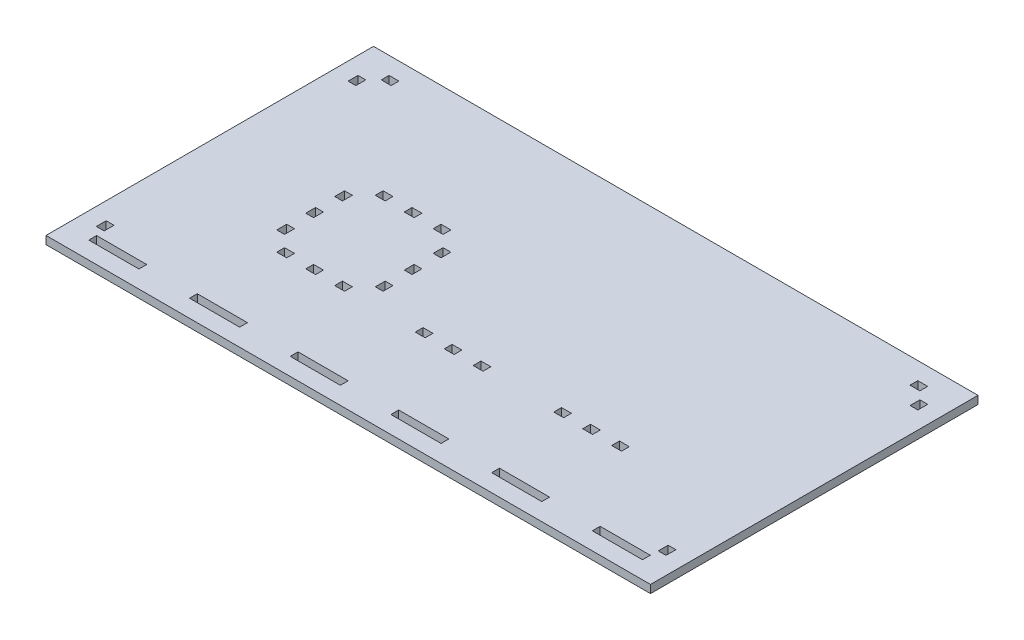
SolidWorks part; units mm, degrees
ref_plane "Front Plane" through (0, 0, 0) normal (0, 0, 1) x (1, 0, 0)
ref_plane "Top Plane" through (0, 0, 0) normal (0, 1, 0) x (1, 0, 0)
ref_plane "Right Plane" through (0, 0, 0) normal (1, 0, 0) x (0, 0, -1)
sketch "Sketch1" plane through (0, 0, 0) normal (0, 1, 0) x (1, 0, 0)
  line L0 (0, 65) -> (0, -65) construction
  line L1 (-120, 65) -> (120, 65)
  line L2 (-120, 65) -> (-120, -65)
  line L3 (-120, -65) -> (120, -65)
  line L4 (120, 65) -> (120, -65)
  line L5 (-111.5875, 55) -> (-111.5875, 45) construction
  line L6 (-113.175, 55) -> (-110, 55) construction
  line L7 (-113.175, 55) -> (-113.175, 45) construction
  line L8 (-113.175, 45) -> (-110, 45) construction
  line L9 (-110, 55) -> (-110, 45) construction
  line L10 (-110, 58.175) -> (-100, 58.175) construction
  line L11 (-110, 58.175) -> (-110, 55) construction
  line L12 (-110, 55) -> (-100, 55) construction
  line L13 (-100, 58.175) -> (-100, 55) construction
  line L14 (-110, 56.5875) -> (-100, 56.5875) construction
  line L15 (100, 56.5875) -> (110, 56.5875) construction
  line L16 (-113.175, 52) -> (-110, 52)
  line L17 (-113.175, 52) -> (-113.175, 48)
  line L18 (-113.175, 48) -> (-110, 48)
  line L19 (-110, 52) -> (-110, 48)
  line L20 (-113.175, 52) -> (-110, 48) construction
  line L21 (-113.175, 48) -> (-110, 52) construction
  line L22 (-107, 55) -> (-103, 55)
  line L23 (-107, 55) -> (-107, 58.175)
  line L24 (-107, 58.175) -> (-103, 58.175)
  line L25 (-103, 55) -> (-103, 58.175)
  line L26 (-107, 55) -> (-103, 58.175) construction
  line L27 (-107, 58.175) -> (-103, 55) construction
  line L28 (110, 55) -> (113.175, 55) construction
  line L29 (110, 55) -> (110, 45) construction
  line L30 (110, 45) -> (113.175, 45) construction
  line L31 (113.175, 55) -> (113.175, 45) construction
  line L32 (100, 58.175) -> (110, 58.175) construction
  line L33 (100, 58.175) -> (100, 55) construction
  line L34 (100, 55) -> (110, 55) construction
  line L35 (110, 58.175) -> (110, 55) construction
  line L36 (111.5875, 55) -> (111.5875, 45) construction
  line L37 (-111.5875, -45) -> (-111.5875, -55) construction
  line L38 (103, 55) -> (107, 55)
  line L39 (103, 55) -> (103, 58.175)
  line L40 (103, 58.175) -> (107, 58.175)
  line L41 (107, 55) -> (107, 58.175)
  line L42 (103, 55) -> (107, 58.175) construction
  line L43 (103, 58.175) -> (107, 55) construction
  line L44 (110, 52) -> (113.175, 52)
  line L45 (110, 52) -> (110, 48)
  line L46 (110, 48) -> (113.175, 48)
  line L47 (113.175, 52) -> (113.175, 48)
  line L48 (110, 52) -> (113.175, 48) construction
  line L49 (110, 48) -> (113.175, 52) construction
  line L50 (-113.175, -45) -> (-110, -45) construction
  line L51 (-113.175, -45) -> (-113.175, -55) construction
  line L52 (-113.175, -55) -> (-110, -55) construction
  line L53 (-110, -45) -> (-110, -55) construction
  line L54 (111.5875, -45) -> (111.5875, -55) construction
  line L55 (-113.175, -52) -> (-110, -52)
  line L56 (-113.175, -52) -> (-113.175, -48)
  line L57 (-113.175, -48) -> (-110, -48)
  line L58 (-110, -52) -> (-110, -48)
  line L59 (-113.175, -52) -> (-110, -48) construction
  line L60 (-113.175, -48) -> (-110, -52) construction
  line L61 (113.175, -55) -> (110, -55) construction
  line L62 (113.175, -55) -> (113.175, -45) construction
  line L63 (113.175, -45) -> (110, -45) construction
  line L64 (110, -55) -> (110, -45) construction
  line L65 (-70, -58.175) -> (-50, -58.175)
  line L66 (110, -52) -> (113.175, -52)
  line L67 (110, -52) -> (110, -48)
  line L68 (110, -48) -> (113.175, -48)
  line L69 (113.175, -52) -> (113.175, -48)
  line L70 (110, -52) -> (113.175, -48) construction
  line L71 (110, -48) -> (113.175, -52) construction
  line L72 (-110, -55) -> (-90, -55)
  line L73 (-110, -55) -> (-110, -58.175)
  line L74 (-110, -58.175) -> (-90, -58.175)
  line L75 (-90, -55) -> (-90, -58.175)
  line L76 (-70, -55) -> (-70, -58.175)
  line L77 (-70, -55) -> (-50, -55)
  line L78 (-50, -55) -> (-50, -58.175)
  line L79 (-30, -58.175) -> (-10, -58.175)
  line L80 (-30, -55) -> (-30, -58.175)
  line L81 (-30, -55) -> (-10, -55)
  line L82 (-10, -55) -> (-10, -58.175)
  line L83 (10, -58.175) -> (30, -58.175)
  line L84 (10, -55) -> (10, -58.175)
  line L85 (10, -55) -> (30, -55)
  line L86 (30, -55) -> (30, -58.175)
  line L87 (50, -58.175) -> (70, -58.175)
  line L88 (50, -55) -> (50, -58.175)
  line L89 (50, -55) -> (70, -55)
  line L90 (70, -55) -> (70, -58.175)
  line L91 (90, -58.175) -> (110, -58.175)
  line L92 (90, -55) -> (90, -58.175)
  line L93 (90, -55) -> (110, -55)
  line L94 (110, -55) -> (110, -58.175)
  line L191 (-68.5, -21.825) -> (-64.5, -21.825)
  line L192 (-68.5, -21.825) -> (-68.5, -25)
  line L193 (-68.5, -25) -> (-64.5, -25)
  line L194 (-64.5, -21.825) -> (-64.5, -25)
  line L195 (-57, -21.825) -> (-53, -21.825)
  line L196 (-57, -21.825) -> (-57, -25)
  line L197 (-57, -25) -> (-53, -25)
  line L198 (-53, -21.825) -> (-53, -25)
  line L199 (-45.5, -21.825) -> (-41.5, -21.825)
  line L200 (-45.5, -21.825) -> (-45.5, -25)
  line L201 (-45.5, -25) -> (-41.5, -25)
  line L202 (-41.5, -21.825) -> (-41.5, -25)
  line L215 (-57, 17.3) -> (-57, 14.125)
  line L216 (41.5, -25) -> (45.5, -25)
  line L217 (41.5, -25) -> (41.5, -21.825)
  line L218 (41.5, -21.825) -> (45.5, -21.825)
  line L219 (45.5, -25) -> (45.5, -21.825)
  line L220 (53, -25) -> (57, -25)
  line L221 (53, -25) -> (53, -21.825)
  line L222 (53, -21.825) -> (57, -21.825)
  line L223 (57, -25) -> (57, -21.825)
  line L224 (64.5, -25) -> (68.5, -25)
  line L225 (64.5, -25) -> (64.5, -21.825)
  line L226 (64.5, -21.825) -> (68.5, -21.825)
  line L227 (68.5, -25) -> (68.5, -21.825)
  line L240 (-13.5, -21.825) -> (-9.5, -21.825)
  line L241 (-13.5, -21.825) -> (-13.5, -25)
  line L242 (-13.5, -25) -> (-9.5, -25)
  line L243 (-9.5, -21.825) -> (-9.5, -25)
  line L244 (-2, -25) -> (2, -25)
  line L245 (-2, -25) -> (-2, -21.825)
  line L246 (-2, -21.825) -> (2, -21.825)
  line L247 (2, -25) -> (2, -21.825)
  line L248 (9.5, -25) -> (13.5, -25)
  line L249 (9.5, -25) -> (9.5, -21.825)
  line L250 (9.5, -21.825) -> (13.5, -21.825)
  line L251 (13.5, -25) -> (13.5, -21.825)
  line L252 (-68.5, 17.3) -> (-68.5, 14.125)
  line L253 (-68.5, 14.125) -> (-64.5, 14.125)
  line L254 (-64.5, 17.3) -> (-64.5, 14.125)
  line L255 (-41.5, 17.3) -> (-41.5, 14.125)
  line L256 (-41.5, 14.125) -> (-45.5, 14.125)
  line L257 (-45.5, 17.3) -> (-45.5, 14.125)
  line L258 (-57, 14.125) -> (-53, 14.125)
  line L259 (-76.15, 17.3) -> (-33.85, 17.3)
  line L260 (-76.15, 17.3) -> (-76.15, -25)
  line L261 (-76.15, -25) -> (-33.85, -25)
  line L262 (-33.85, 17.3) -> (-33.85, -25)
  line L263 (-76.15, 17.3) -> (-33.85, -25) construction
  line L264 (-76.15, -25) -> (-33.85, 17.3) construction
  line L265 (-53, 17.3) -> (-53, 14.125)
  line L266 (-57, 17.3) -> (-53, 14.125) construction
  line L267 (-57, 14.125) -> (-53, 17.3) construction
  line L268 (-57, 17.3) -> (-53, 17.3)
  line L269 (-57, -21.825) -> (-57, -25)
  line L270 (-68.5, -21.825) -> (-68.5, -25)
  line L271 (-68.5, -25) -> (-64.5, -25)
  line L272 (-64.5, -21.825) -> (-64.5, -25)
  line L273 (-41.5, -21.825) -> (-41.5, -25)
  line L274 (-41.5, -25) -> (-45.5, -25)
  line L275 (-45.5, -21.825) -> (-45.5, -25)
  line L276 (-57, -25) -> (-53, -25)
  line L277 (-53, -21.825) -> (-53, -25)
  line L278 (-57, -21.825) -> (-53, -25) construction
  line L279 (-57, -25) -> (-53, -21.825) construction
  line L280 (-57, -21.825) -> (-53, -21.825)
  line L281 (-45.5, -21.825) -> (-41.5, -21.825)
  line L282 (-68.5, -21.825) -> (-64.5, -21.825)
  line L283 (-76.15, -5.85) -> (-72.975, -5.85)
  line L284 (-76.15, -5.85) -> (-76.15, -1.85)
  line L285 (-76.15, -1.85) -> (-72.975, -1.85)
  line L286 (-72.975, -5.85) -> (-72.975, -1.85)
  line L287 (-76.15, 5.65) -> (-72.975, 5.65)
  line L288 (-76.15, 5.65) -> (-76.15, 9.65)
  line L289 (-76.15, 9.65) -> (-72.975, 9.65)
  line L290 (-72.975, 5.65) -> (-72.975, 9.65)
  line L291 (-55, 17.3) -> (-55, -25) construction
  line L292 (-76.15, -13.35) -> (-72.975, -13.35)
  line L293 (-76.15, -13.35) -> (-76.15, -17.35)
  line L294 (-76.15, -17.35) -> (-72.975, -17.35)
  line L295 (-72.975, -13.35) -> (-72.975, -17.35)
  line L296 (-37.025, -13.35) -> (-37.025, -17.35)
  line L297 (-33.85, -17.35) -> (-37.025, -17.35)
  line L298 (-33.85, -13.35) -> (-37.025, -13.35)
  line L299 (-37.025, 5.65) -> (-37.025, 9.65)
  line L300 (-33.85, 9.65) -> (-37.025, 9.65)
  line L301 (-33.85, 5.65) -> (-37.025, 5.65)
  line L302 (-37.025, -5.85) -> (-37.025, -1.85)
  line L303 (-33.85, -1.85) -> (-37.025, -1.85)
  line L304 (-33.85, -5.85) -> (-37.025, -5.85)
  point P19 (-111.5875, 50)
  point P24 (-105, 56.5875)
  point P41 (105, 56.5875)
  point P46 (111.5875, 50)
  point P57 (-111.5875, -50)
  point P68 (111.5875, -50)
  point P77 (-55, -25)
  point P121 (55, -25)
  point P134 (0, -25)
  point P135 (-55, -25)
  point P144 (-55, 15.7125)
  point P148 (-55, -3.85)
  point P155 (-55, -25)
  point P156 (-55, 17.3)
  point P157 (-55, 17.3)
  point P166 (-55, -23.4125)
  point P182 (-72.975, -3.85)
  point P183 (-76.15, -3.85)
  dimension "D1" = 240
  dimension "D2" = 130
  dimension "D3" = 65
  dimension "D4" = 120
  dimension "D5" = 6.825
  dimension "D6" = 6.825
  dimension "D7" = 10
  dimension "D8" = 10
  dimension "D9" = 3.175
  dimension "D10" = 10
  dimension "D11" = 4
  dimension "D12" = 4
  dimension "D13" = 6.825
  dimension "D14" = 6.825
  dimension "D15" = 10
  dimension "D16" = 10
  dimension "D17" = 10
  dimension "D18" = 3.175
  dimension "D19" = 4
  dimension "D20" = 4
  dimension "D21" = 6.825
  dimension "D22" = 10
  dimension "D23" = 10
  dimension "D24" = 3.175
  dimension "D25" = 4
  dimension "D26" = 6.825
  dimension "D27" = 3.175
  dimension "D28" = 10
  dimension "D29" = 10
  dimension "D30" = 4
  dimension "D31" = 20
  dimension "D32" = 3.175
  dimension "D37" = 4
  dimension "D39" = 3.175
  dimension "D34" = 7.5
  dimension "D35" = 7.5
  dimension "D36" = 55
  dimension "D38" = 4
  dimension "D40" = 3.175
  dimension "D41" = 7.5
  dimension "D42" = 7.5
  dimension "D43" = 55
  dimension "D44" = 30
  dimension "D45" = 30
  dimension "D46" = 4
  dimension "D47" = 3.175
  dimension "D48" = 7.5
  dimension "D49" = 7.5
  dimension "D50" = 30
  dimension "D51" = 42.3
  dimension "D52" = 42.3
  dimension "D53" = 4
  dimension "D54" = 3.175
  dimension "D55" = 7.5
  dimension "D56" = 7.5
  dimension "D57" = 4
  dimension "D58" = 3.175
  dimension "D59" = 7.5
  dimension "D60" = 7.5
  dimension "D61" = 3.175
  dimension "D62" = 7.5
  dimension "D63" = 7.5
  dimension "D33" = 6
extrude "Boss-Extrude1" add sketch "Sketch1" along normal blind 3.175 contours L4 L1 L2 L3 L251 L248 L249 L250 L247 L244 L245 L246 L227 L224 L225 L226 L223 L220 L221 L222 L219 L216 L217 L218 L69 L66 L67 L68 L58 L55 L56 L57 L41 L38 L39 L40 L25 L22 L23 L24 L16 | L262 L304 L302 L303 L301 L299 L300 L259 L255 L256 L257 L265 L258 L215 L254 L253 L252 L260 L289 L290 L287 L285 L286 L283 L292 L295 L294 L261 L192 L191 L194 L196 L195 L198 L200 L199 L202 L297 L296
sketch "Sketch2" plane through (0, 3.175, 0) normal (0, 1, 0) x (1, 0, 0)
  line L8 (120.0406, -65.0406) -> (120.0406, 65.0406)
  line L9 (120.0406, 65.0406) -> (-120.0406, 65.0406)
  line L10 (-120.0406, 65.0406) -> (-120.0406, -65.0406)
  line L11 (-120.0406, -65.0406) -> (120.0406, -65.0406)
  line L12 (120.0406, -65.0406) -> (120.0406, 65.0406)
  line L13 (120.0406, 65.0406) -> (-120.0406, 65.0406)
  line L14 (-120.0406, 65.0406) -> (-120.0406, -65.0406)
  line L15 (-120.0406, -65.0406) -> (120.0406, -65.0406)
  line L21 (-33.8906, 5.6906) -> (-33.8906, 9.6094)
  line L22 (-73.0156, -1.8906) -> (-76.1094, -1.8906)
  line L23 (-73.0156, -5.8094) -> (-73.0156, -1.8906)
  line L24 (-76.1094, -5.8094) -> (-73.0156, -5.8094)
  line L25 (-76.1094, -1.8906) -> (-76.1094, -5.8094)
  line L26 (-103.0406, 55.0406) -> (-103.0406, 58.1344)
  line L27 (-106.9594, 55.0406) -> (-103.0406, 55.0406)
  line L28 (-106.9594, 58.1344) -> (-106.9594, 55.0406)
  line L29 (-103.0406, 58.1344) -> (-106.9594, 58.1344)
  line L30 (-103.0406, 55.0406) -> (-103.0406, 58.1344)
  line L31 (-106.9594, 55.0406) -> (-103.0406, 55.0406)
  line L32 (-106.9594, 58.1344) -> (-106.9594, 55.0406)
  line L33 (-103.0406, 58.1344) -> (-106.9594, 58.1344)
  line L34 (-73.0156, -1.8906) -> (-76.1094, -1.8906)
  line L35 (-73.0156, -5.8094) -> (-73.0156, -1.8906)
  line L36 (-76.1094, -5.8094) -> (-73.0156, -5.8094)
  line L37 (-76.1094, -1.8906) -> (-76.1094, -5.8094)
  line L38 (-36.9844, 5.6906) -> (-33.8906, 5.6906)
  line L39 (-33.8906, 9.6094) -> (-36.9844, 9.6094)
  line L40 (-36.9844, 9.6094) -> (-36.9844, 5.6906)
  line L41 (-33.8906, 5.6906) -> (-33.8906, 9.6094)
  line L42 (-36.9844, 5.6906) -> (-33.8906, 5.6906)
  line L43 (-33.8906, 9.6094) -> (-36.9844, 9.6094)
  line L44 (-113.1344, 48.0406) -> (-110.0406, 48.0406)
  line L45 (-110.0406, 48.0406) -> (-110.0406, 51.9594)
  line L46 (-110.0406, 51.9594) -> (-113.1344, 51.9594)
  line L47 (-113.1344, 51.9594) -> (-113.1344, 48.0406)
  line L48 (-113.1344, 48.0406) -> (-110.0406, 48.0406)
  line L49 (-110.0406, 48.0406) -> (-110.0406, 51.9594)
  line L50 (-110.0406, 51.9594) -> (-113.1344, 51.9594)
  line L51 (-113.1344, 51.9594) -> (-113.1344, 48.0406)
  line L52 (-36.9844, 9.6094) -> (-36.9844, 5.6906)
  line L54 (-9.5406, -24.9594) -> (-9.5406, -21.8656)
  line L55 (-13.4594, -24.9594) -> (-9.5406, -24.9594)
  line L56 (-73.0156, -17.3094) -> (-73.0156, -13.3906)
  line L57 (-76.1094, -13.3906) -> (-76.1094, -17.3094)
  line L58 (-76.1094, -17.3094) -> (-73.0156, -17.3094)
  line L59 (-73.0156, -13.3906) -> (-76.1094, -13.3906)
  line L60 (-73.0156, -17.3094) -> (-73.0156, -13.3906)
  line L61 (-76.1094, -13.3906) -> (-76.1094, -17.3094)
  line L62 (103.0406, 55.0406) -> (106.9594, 55.0406)
  line L63 (103.0406, 58.1344) -> (103.0406, 55.0406)
  line L64 (106.9594, 58.1344) -> (103.0406, 58.1344)
  line L65 (106.9594, 55.0406) -> (106.9594, 58.1344)
  line L66 (103.0406, 55.0406) -> (106.9594, 55.0406)
  line L67 (103.0406, 58.1344) -> (103.0406, 55.0406)
  line L68 (106.9594, 58.1344) -> (103.0406, 58.1344)
  line L69 (106.9594, 55.0406) -> (106.9594, 58.1344)
  line L70 (-76.1094, -17.3094) -> (-73.0156, -17.3094)
  line L71 (-73.0156, -13.3906) -> (-76.1094, -13.3906)
  line L72 (-13.4594, -21.8656) -> (-13.4594, -24.9594)
  line L73 (-9.5406, -21.8656) -> (-13.4594, -21.8656)
  line L74 (-9.5406, -24.9594) -> (-9.5406, -21.8656)
  line L75 (-13.4594, -24.9594) -> (-9.5406, -24.9594)
  line L76 (-13.4594, -21.8656) -> (-13.4594, -24.9594)
  line L77 (-9.5406, -21.8656) -> (-13.4594, -21.8656)
  line L79 (-33.8906, -5.8094) -> (-33.8906, -1.8906)
  line L80 (110.0406, 48.0406) -> (113.1344, 48.0406)
  line L81 (110.0406, 51.9594) -> (110.0406, 48.0406)
  line L82 (113.1344, 48.0406) -> (113.1344, 51.9594)
  line L83 (113.1344, 51.9594) -> (110.0406, 51.9594)
  line L84 (110.0406, 48.0406) -> (113.1344, 48.0406)
  line L85 (110.0406, 51.9594) -> (110.0406, 48.0406)
  line L86 (113.1344, 48.0406) -> (113.1344, 51.9594)
  line L87 (113.1344, 51.9594) -> (110.0406, 51.9594)
  line L88 (-36.9844, -1.8906) -> (-36.9844, -5.8094)
  line L89 (-36.9844, -5.8094) -> (-33.8906, -5.8094)
  line L90 (-64.5406, 14.1656) -> (-64.5406, 17.2594)
  line L91 (-68.4594, 17.2594) -> (-68.4594, 14.1656)
  line L92 (-68.4594, 14.1656) -> (-64.5406, 14.1656)
  line L93 (-64.5406, 17.2594) -> (-68.4594, 17.2594)
  line L94 (-64.5406, 14.1656) -> (-64.5406, 17.2594)
  line L95 (-68.4594, 17.2594) -> (-68.4594, 14.1656)
  line L96 (-68.4594, 14.1656) -> (-64.5406, 14.1656)
  line L97 (-64.5406, 17.2594) -> (-68.4594, 17.2594)
  line L98 (-33.8906, -1.8906) -> (-36.9844, -1.8906)
  line L99 (-33.8906, -5.8094) -> (-33.8906, -1.8906)
  line L100 (-36.9844, -1.8906) -> (-36.9844, -5.8094)
  line L101 (-36.9844, -5.8094) -> (-33.8906, -5.8094)
  line L102 (-33.8906, -1.8906) -> (-36.9844, -1.8906)
  line L108 (-110.0406, -51.9594) -> (-110.0406, -48.0406)
  line L109 (-113.1344, -51.9594) -> (-110.0406, -51.9594)
  line L110 (-113.1344, -48.0406) -> (-113.1344, -51.9594)
  line L111 (-110.0406, -48.0406) -> (-113.1344, -48.0406)
  line L112 (-110.0406, -51.9594) -> (-110.0406, -48.0406)
  line L113 (-113.1344, -51.9594) -> (-110.0406, -51.9594)
  line L114 (-113.1344, -48.0406) -> (-113.1344, -51.9594)
  line L115 (-110.0406, -48.0406) -> (-113.1344, -48.0406)
  line L116 (-53.0406, 14.1656) -> (-53.0406, 17.2594)
  line L117 (-56.9594, 17.2594) -> (-56.9594, 14.1656)
  line L118 (-56.9594, 14.1656) -> (-53.0406, 14.1656)
  line L119 (-53.0406, 17.2594) -> (-56.9594, 17.2594)
  line L120 (-53.0406, 14.1656) -> (-53.0406, 17.2594)
  line L121 (-56.9594, 17.2594) -> (-56.9594, 14.1656)
  line L122 (-56.9594, 14.1656) -> (-53.0406, 14.1656)
  line L123 (-53.0406, 17.2594) -> (-56.9594, 17.2594)
  line L126 (-109.9594, -55.0406) -> (-109.9594, -58.1344)
  line L127 (-90.0406, -58.1344) -> (-90.0406, -55.0406)
  line L128 (-109.9594, -58.1344) -> (-90.0406, -58.1344)
  line L129 (-90.0406, -55.0406) -> (-109.9594, -55.0406)
  line L130 (-109.9594, -55.0406) -> (-109.9594, -58.1344)
  line L131 (-90.0406, -58.1344) -> (-90.0406, -55.0406)
  line L132 (-109.9594, -58.1344) -> (-90.0406, -58.1344)
  line L133 (-90.0406, -55.0406) -> (-109.9594, -55.0406)
  line L136 (-1.9594, -24.9594) -> (1.9594, -24.9594)
  line L137 (-33.8906, -17.3094) -> (-33.8906, -13.3906)
  line L138 (-36.9844, -17.3094) -> (-33.8906, -17.3094)
  line L139 (-36.9844, -13.3906) -> (-36.9844, -17.3094)
  line L140 (-33.8906, -13.3906) -> (-36.9844, -13.3906)
  line L141 (-33.8906, -17.3094) -> (-33.8906, -13.3906)
  line L142 (-41.5406, 14.1656) -> (-41.5406, 17.2594)
  line L143 (-45.4594, 17.2594) -> (-45.4594, 14.1656)
  line L144 (-50.0406, -58.1344) -> (-50.0406, -55.0406)
  line L145 (-69.9594, -55.0406) -> (-69.9594, -58.1344)
  line L146 (-69.9594, -58.1344) -> (-50.0406, -58.1344)
  line L147 (-50.0406, -55.0406) -> (-69.9594, -55.0406)
  line L148 (-50.0406, -58.1344) -> (-50.0406, -55.0406)
  line L149 (-69.9594, -55.0406) -> (-69.9594, -58.1344)
  line L150 (-69.9594, -58.1344) -> (-50.0406, -58.1344)
  line L151 (-50.0406, -55.0406) -> (-69.9594, -55.0406)
  line L152 (-41.5406, 17.2594) -> (-45.4594, 17.2594)
  line L153 (-45.4594, 14.1656) -> (-41.5406, 14.1656)
  line L154 (-41.5406, 14.1656) -> (-41.5406, 17.2594)
  line L155 (-45.4594, 17.2594) -> (-45.4594, 14.1656)
  line L156 (-41.5406, 17.2594) -> (-45.4594, 17.2594)
  line L157 (-45.4594, 14.1656) -> (-41.5406, 14.1656)
  line L158 (-36.9844, -17.3094) -> (-33.8906, -17.3094)
  line L159 (-36.9844, -13.3906) -> (-36.9844, -17.3094)
  line L160 (-33.8906, -13.3906) -> (-36.9844, -13.3906)
  line L161 (1.9594, -24.9594) -> (1.9594, -21.8656)
  line L162 (-10.0406, -58.1344) -> (-10.0406, -55.0406)
  line L163 (-29.9594, -58.1344) -> (-10.0406, -58.1344)
  line L164 (-29.9594, -55.0406) -> (-29.9594, -58.1344)
  line L165 (-10.0406, -55.0406) -> (-29.9594, -55.0406)
  line L166 (-10.0406, -58.1344) -> (-10.0406, -55.0406)
  line L167 (-29.9594, -58.1344) -> (-10.0406, -58.1344)
  line L168 (-29.9594, -55.0406) -> (-29.9594, -58.1344)
  line L169 (-10.0406, -55.0406) -> (-29.9594, -55.0406)
  line L170 (-1.9594, -21.8656) -> (-1.9594, -24.9594)
  line L171 (1.9594, -21.8656) -> (-1.9594, -21.8656)
  line L172 (-1.9594, -24.9594) -> (1.9594, -24.9594)
  line L173 (1.9594, -24.9594) -> (1.9594, -21.8656)
  line L174 (-1.9594, -21.8656) -> (-1.9594, -24.9594)
  line L175 (1.9594, -21.8656) -> (-1.9594, -21.8656)
  line L176 (-64.5406, -24.9594) -> (-64.5406, -21.8656)
  line L177 (-68.4594, -21.8656) -> (-68.4594, -24.9594)
  line L178 (-64.5406, -21.8656) -> (-68.4594, -21.8656)
  line L179 (-68.4594, -24.9594) -> (-64.5406, -24.9594)
  line L180 (29.9594, -58.1344) -> (29.9594, -55.0406)
  line L181 (10.0406, -55.0406) -> (10.0406, -58.1344)
  line L182 (10.0406, -58.1344) -> (29.9594, -58.1344)
  line L183 (29.9594, -55.0406) -> (10.0406, -55.0406)
  line L184 (29.9594, -58.1344) -> (29.9594, -55.0406)
  line L185 (10.0406, -55.0406) -> (10.0406, -58.1344)
  line L186 (10.0406, -58.1344) -> (29.9594, -58.1344)
  line L187 (29.9594, -55.0406) -> (10.0406, -55.0406)
  line L188 (-64.5406, -24.9594) -> (-64.5406, -21.8656)
  line L189 (-68.4594, -21.8656) -> (-68.4594, -24.9594)
  line L190 (-64.5406, -21.8656) -> (-68.4594, -21.8656)
  line L191 (-68.4594, -24.9594) -> (-64.5406, -24.9594)
  line L198 (69.9594, -58.1344) -> (69.9594, -55.0406)
  line L199 (50.0406, -55.0406) -> (50.0406, -58.1344)
  line L200 (69.9594, -55.0406) -> (50.0406, -55.0406)
  line L201 (50.0406, -58.1344) -> (69.9594, -58.1344)
  line L202 (69.9594, -58.1344) -> (69.9594, -55.0406)
  line L203 (50.0406, -55.0406) -> (50.0406, -58.1344)
  line L204 (69.9594, -55.0406) -> (50.0406, -55.0406)
  line L205 (50.0406, -58.1344) -> (69.9594, -58.1344)
  line L206 (-56.9594, -24.9594) -> (-53.0406, -24.9594)
  line L207 (-53.0406, -24.9594) -> (-53.0406, -21.8656)
  line L208 (-53.0406, -21.8656) -> (-56.9594, -21.8656)
  line L209 (-56.9594, -21.8656) -> (-56.9594, -24.9594)
  line L210 (-56.9594, -24.9594) -> (-53.0406, -24.9594)
  line L211 (-53.0406, -24.9594) -> (-53.0406, -21.8656)
  line L212 (-53.0406, -21.8656) -> (-56.9594, -21.8656)
  line L213 (-56.9594, -21.8656) -> (-56.9594, -24.9594)
  line L218 (13.4594, -24.9594) -> (13.4594, -21.8656)
  line L219 (9.5406, -24.9594) -> (13.4594, -24.9594)
  line L220 (109.9594, -58.1344) -> (109.9594, -55.0406)
  line L221 (90.0406, -55.0406) -> (90.0406, -58.1344)
  line L222 (90.0406, -58.1344) -> (109.9594, -58.1344)
  line L223 (109.9594, -55.0406) -> (90.0406, -55.0406)
  line L224 (109.9594, -58.1344) -> (109.9594, -55.0406)
  line L225 (90.0406, -55.0406) -> (90.0406, -58.1344)
  line L226 (90.0406, -58.1344) -> (109.9594, -58.1344)
  line L227 (109.9594, -55.0406) -> (90.0406, -55.0406)
  line L229 (9.5406, -21.8656) -> (9.5406, -24.9594)
  line L230 (13.4594, -21.8656) -> (9.5406, -21.8656)
  line L231 (13.4594, -24.9594) -> (13.4594, -21.8656)
  line L232 (-45.4594, -24.9594) -> (-41.5406, -24.9594)
  line L233 (-41.5406, -24.9594) -> (-41.5406, -21.8656)
  line L234 (-45.4594, -21.8656) -> (-45.4594, -24.9594)
  line L235 (-41.5406, -21.8656) -> (-45.4594, -21.8656)
  line L236 (-45.4594, -24.9594) -> (-41.5406, -24.9594)
  line L237 (-41.5406, -24.9594) -> (-41.5406, -21.8656)
  line L238 (113.1344, -51.9594) -> (113.1344, -48.0406)
  line L239 (110.0406, -51.9594) -> (113.1344, -51.9594)
  line L240 (110.0406, -48.0406) -> (110.0406, -51.9594)
  line L241 (113.1344, -48.0406) -> (110.0406, -48.0406)
  line L242 (113.1344, -51.9594) -> (113.1344, -48.0406)
  line L243 (110.0406, -51.9594) -> (113.1344, -51.9594)
  line L244 (110.0406, -48.0406) -> (110.0406, -51.9594)
  line L245 (113.1344, -48.0406) -> (110.0406, -48.0406)
  line L246 (-45.4594, -21.8656) -> (-45.4594, -24.9594)
  line L247 (-41.5406, -21.8656) -> (-45.4594, -21.8656)
  line L248 (9.5406, -24.9594) -> (13.4594, -24.9594)
  line L249 (9.5406, -21.8656) -> (9.5406, -24.9594)
  line L250 (13.4594, -21.8656) -> (9.5406, -21.8656)
  line L261 (45.4594, -24.9594) -> (45.4594, -21.8656)
  line L262 (45.4594, -21.8656) -> (41.5406, -21.8656)
  line L263 (41.5406, -21.8656) -> (41.5406, -24.9594)
  line L264 (41.5406, -24.9594) -> (45.4594, -24.9594)
  line L265 (-76.1094, 5.6906) -> (-73.0156, 5.6906)
  line L266 (-73.0156, 5.6906) -> (-73.0156, 9.6094)
  line L267 (-76.1094, 9.6094) -> (-76.1094, 5.6906)
  line L268 (-73.0156, 9.6094) -> (-76.1094, 9.6094)
  line L269 (-76.1094, 5.6906) -> (-73.0156, 5.6906)
  line L270 (-73.0156, 5.6906) -> (-73.0156, 9.6094)
  line L271 (-76.1094, 9.6094) -> (-76.1094, 5.6906)
  line L272 (-73.0156, 9.6094) -> (-76.1094, 9.6094)
  line L273 (45.4594, -24.9594) -> (45.4594, -21.8656)
  line L274 (45.4594, -21.8656) -> (41.5406, -21.8656)
  line L275 (41.5406, -21.8656) -> (41.5406, -24.9594)
  line L276 (41.5406, -24.9594) -> (45.4594, -24.9594)
  line L291 (56.9594, -24.9594) -> (56.9594, -21.8656)
  line L292 (53.0406, -24.9594) -> (56.9594, -24.9594)
  line L293 (56.9594, -21.8656) -> (53.0406, -21.8656)
  line L294 (53.0406, -21.8656) -> (53.0406, -24.9594)
  line L295 (56.9594, -24.9594) -> (56.9594, -21.8656)
  line L296 (53.0406, -24.9594) -> (56.9594, -24.9594)
  line L297 (56.9594, -21.8656) -> (53.0406, -21.8656)
  line L298 (53.0406, -21.8656) -> (53.0406, -24.9594)
  line L309 (68.4594, -24.9594) -> (68.4594, -21.8656)
  line L310 (64.5406, -24.9594) -> (68.4594, -24.9594)
  line L311 (64.5406, -21.8656) -> (64.5406, -24.9594)
  line L312 (68.4594, -21.8656) -> (64.5406, -21.8656)
  line L313 (68.4594, -24.9594) -> (68.4594, -21.8656)
  line L314 (64.5406, -24.9594) -> (68.4594, -24.9594)
  line L315 (64.5406, -21.8656) -> (64.5406, -24.9594)
  line L316 (68.4594, -21.8656) -> (64.5406, -21.8656)
  dimension "D1" = 0.0406
  dimension "D2" = 0.0406
  dimension "D3" = 0.0406
  dimension "D4" = 0.0406
  dimension "D5" = 0.0406
  dimension "D6" = 0.0406
  dimension "D7" = 0.0406
  dimension "D8" = 0.0406
  dimension "D9" = 0.0406
  dimension "D10" = 0.0406
  dimension "D11" = 0.0406
  dimension "D12" = 0.0406
  dimension "D13" = 0.0406
  dimension "D14" = 0.0406
  dimension "D15" = 0.0406
  dimension "D16" = 0.0406
  dimension "D17" = 0.0406
  dimension "D18" = 0.0406
  dimension "D19" = 0.0406
  dimension "D20" = 0.0406
  dimension "D21" = 0.0406
  dimension "D22" = 0.0406
  dimension "D23" = 0.0406
  dimension "D24" = 0.0406
  dimension "D25" = 0.0406
  dimension "D26" = 0.0406
  dimension "D27" = 0.0406
  dimension "D28" = 0.0406
  dimension "D29" = 0.0406
  dimension "D30" = 0.0406
  dimension "D31" = 0.0406
extrude "Boss-Extrude2" add sketch "Sketch2" against normal blind 3.175
equation "\"stepper width\"=4.23"
equation "\"stepper hole disctance\"= 3.1"
equation "\"stepper hole diameter\"=0.34"
equation "\"stepper shaft hole\"=2.4"
equation "\"tooth width\"=0.4"
equation "\"tooth thickness\"=0.3175"
equation "\"tooth to side\"=0.75"
equation "\"motor chamber height\"= 6"
equation "\"enclosure length\"= 22"
equation "\"platform diameter\"= 9cm"
equation "\"teeth width\"=0.3175"
equation "\"teeth lenght\"=2"
equation "\"tower width\"=7.7"
equation "\"D1@Sketch1\"=\"enclosure length\"+2"
equation "\"D2@Sketch1\"=\"enclosure length\"/2+2"
equation "\"D3@Sketch1\"=\"enclosure length\"/4+1"
equation "\"D4@Sketch1\"=\"enclosure length\"/2+1"
equation "\"D5@Sketch1\"=1 - \"tooth thickness\""
equation "\"D6@Sketch1\"=1 - \"tooth thickness\""
equation "\"D9@Sketch1\"=\"teeth width\""
equation "\"support width\"=1"
equation "\"D10@Sketch1\"=\"support width\""
equation "\"D11@Sketch1\"=\"tooth width\""
equation "\"D12@Sketch1\"=\"tooth width\""
equation "\"D13@Sketch1\"=1 - \"tooth thickness\""
equation "\"D14@Sketch1\"=1 - \"tooth thickness\""
equation "\"D17@Sketch1\"=\"support width\""
equation "\"D18@Sketch1\"=\"tooth thickness\""
equation "\"D19@Sketch1\"=\"tooth width\""
equation "\"D20@Sketch1\"=\"tooth width\""
equation "\"D21@Sketch1\"=1 - \"tooth thickness\""
equation "\"D23@Sketch1\"=\"support width\""
equation "\"D24@Sketch1\"=\"tooth thickness\""
equation "\"D25@Sketch1\"=\"tooth width\""
equation "\"D26@Sketch1\"=1 - \"tooth thickness\""
equation "\"D27@Sketch1\"=\"tooth thickness\""
equation "\"D28@Sketch1\"=\"support width\""
equation "\"D30@Sketch1\"=\"tooth width\""
equation "\"D31@Sketch1\"=\"teeth lenght\""
equation "\"D32@Sketch1\"=\"tooth thickness\""
equation "\"trial hole spacing\"= 0.75"
equation "\"mounting distance\"= 4"
equation "\"D1@Boss-Extrude1\"=\"tooth thickness\""
equation "\"D37@Sketch1\"=\"tooth width\""
equation "\"D39@Sketch1\"=\"tooth thickness\""
equation "\"D34@Sketch1\"=\"tooth to side\""
equation "\"half belt distance\"=5.5"
equation "\"D36@Sketch1\"=\"half belt distance\""
equation "\"D38@Sketch1\"=\"tooth width\""
equation "\"D40@Sketch1\"=\"tooth thickness\""
equation "\"D41@Sketch1\"=\"tooth to side\""
equation "\"D42@Sketch1\"=\"tooth to side\""
equation "\"D43@Sketch1\"=\"half belt distance\""
equation "\"holder distance to wall\"=3"
equation "\"D44@Sketch1\"=\"holder distance to wall\""
equation "\"D45@Sketch1\"=\"holder distance to wall\""
equation "\"D46@Sketch1\"=\"tooth width\""
equation "\"D47@Sketch1\"=\"tooth thickness\""
equation "\"D48@Sketch1\"=\"tooth to side\""
equation "\"D49@Sketch1\"=\"tooth to side\""
equation "\"D50@Sketch1\"=\"holder distance to wall\""
